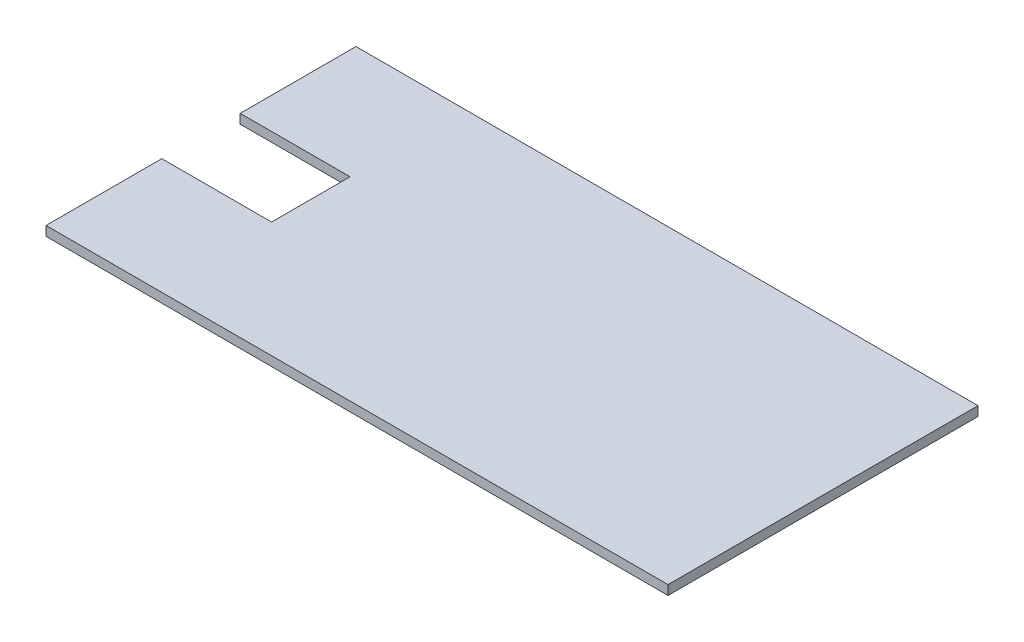
SolidWorks part; units mm, degrees
ref_plane "Front Plane" through (0, 0, 0) normal (0, 0, 1) x (1, 0, 0)
ref_plane "Top Plane" through (0, 0, 0) normal (0, 1, 0) x (1, 0, 0)
ref_plane "Right Plane" through (0, 0, 0) normal (1, 0, 0) x (0, 0, -1)
sketch "Sketch1" plane through (0, 0, 0) normal (0, 1, 0) x (1, 0, 0)
  line L0 (-60.5782, -33.3961) -> (-60.5782, -70.2961)
  line L1 (-60.5782, 28.5039) -> (137.6818, 28.5039)
  line L2 (-60.5782, 28.5039) -> (-60.5782, -8.3961)
  line L3 (-60.5782, -70.2961) -> (137.6818, -70.2961)
  line L4 (137.6818, 28.5039) -> (137.6818, -70.2961)
  line L5 (-60.5782, -8.3961) -> (-25.5782, -8.3961)
  line L7 (-60.5782, -33.3961) -> (-25.5782, -33.3961)
  line L8 (-25.5782, -8.3961) -> (-25.5782, -33.3961)
  point P8 (0, 0)
  dimension "D1" = 198.26
  dimension "D2" = 98.8
  dimension "D3" = 35
  dimension "D4" = 25
extrude "Boss-Extrude1" add sketch "Sketch1" along normal blind 3
equation "\"Fit\"= 1"
equation "\"cover width\"= 98.8"
equation "\"bottom 7 length\"= 198.26"
equation "\"thinner acrylic\"= 3"
equation "\"D1@Sketch1\"=\"bottom 7 length\""
equation "\"D2@Sketch1\"=\"cover width\""
equation "\"D1@Boss-Extrude1\"=\"thinner acrylic\""
equation "\"camera hole width\"= 25"
equation "\"camera hole length\"= 35"
equation "\"camera hole from bottom\"= 185"
equation "\"D3@Sketch1\"=\"camera hole length\""
equation "\"D4@Sketch1\"=\"camera hole width\""
